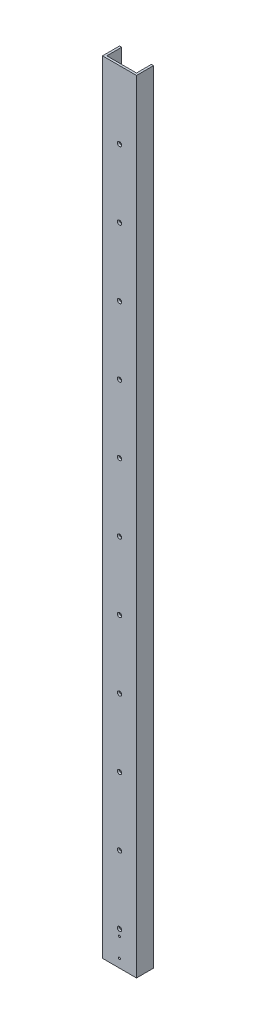
SolidWorks part; units mm, degrees
ref_plane "Front" through (0, 0, 0) normal (0, 0, 1) x (1, 0, 0)
ref_plane "Top" through (0, 0, 0) normal (0, 1, 0) x (1, 0, 0)
ref_plane "Right" through (0, 0, 0) normal (1, 0, 0) x (0, 0, -1)
sketch "Sketch1" plane through (0, 0, 0) normal (0, 1, 0) x (1, 0, 0)
  line L0 (3.175, 3.175) -> (3.175, 25.4)
  line L1 (0, 0) -> (50.8, 0)
  line L2 (0, 0) -> (0, 25.4)
  line L4 (50.8, 0) -> (50.8, 25.4)
  line L5 (3.175, 3.175) -> (47.625, 3.175)
  line L6 (47.625, 3.175) -> (47.625, 25.4)
  line L7 (0, 25.4) -> (3.175, 25.4)
  line L8 (50.8, 25.4) -> (47.625, 25.4)
  dimension "D1" = 25.4
  dimension "D2" = 50.8
  dimension "D3" = 3.175
extrude "Boss-Extrude1" add sketch "Sketch1" along normal blind 1168.4
sketch "Sketch2" plane through (0, 0, 0) normal (0, 0, 1) x (1, 0, 0)
  line L0 (25.4, 0) -> (25.4, 50.8) construction
  line L1 (0, 0) -> (50.8, 0) construction
  circle A0 centre (25.4, 50.8) radius 3.175
  circle A1 centre (25.4, 152.4) radius 3.175
  circle A2 centre (25.4, 254) radius 3.175
  circle A3 centre (25.4, 355.6) radius 3.175
  circle A4 centre (25.4, 457.2) radius 3.175
  circle A5 centre (25.4, 558.8) radius 3.175
  circle A6 centre (25.4, 660.4) radius 3.175
  circle A7 centre (25.4, 762) radius 3.175
  circle A8 centre (25.4, 863.6) radius 3.175
  circle A9 centre (25.4, 965.2) radius 3.175
  circle A10 centre (25.4, 1066.8) radius 3.175
  dimension "D2" = 6.35
  dimension "D1" = 50.8
  dimension "D3" = 11
extrude "Cut-Extrude1" cut sketch "Sketch2" against normal up to next
sketch "Sketch4" plane through (0, 0, 0) normal (0, 0, 1) x (1, 0, 0)
  line L0 (25.4, 41.275) -> (50.8, 41.275) construction
  line L1 (50.8, 1168.4) -> (50.8, 0) construction
  line L2 (25.4, 41.275) -> (0, 41.275) construction
  line L3 (0, 1168.4) -> (0, 0) construction
  line L4 (25.4, 41.275) -> (25.4, 12.7) construction
  line L5 (25.4, 12.7) -> (25.4, 0) construction
  line L6 (0, 0) -> (50.8, 0) construction
  circle A1 centre (25.4, 41.275) radius 1.5875
  circle A3 centre (25.4, 12.7) radius 1.5875
  dimension "D1" = 28.575
  dimension "D2" = 12.7
extrude "Cut-Extrude2" cut sketch "Sketch4" against normal up to next
ref_plane "Mid_Plane" through (25.4, 0, 0) normal (1, 0, 0) x (0, 0, -1)
